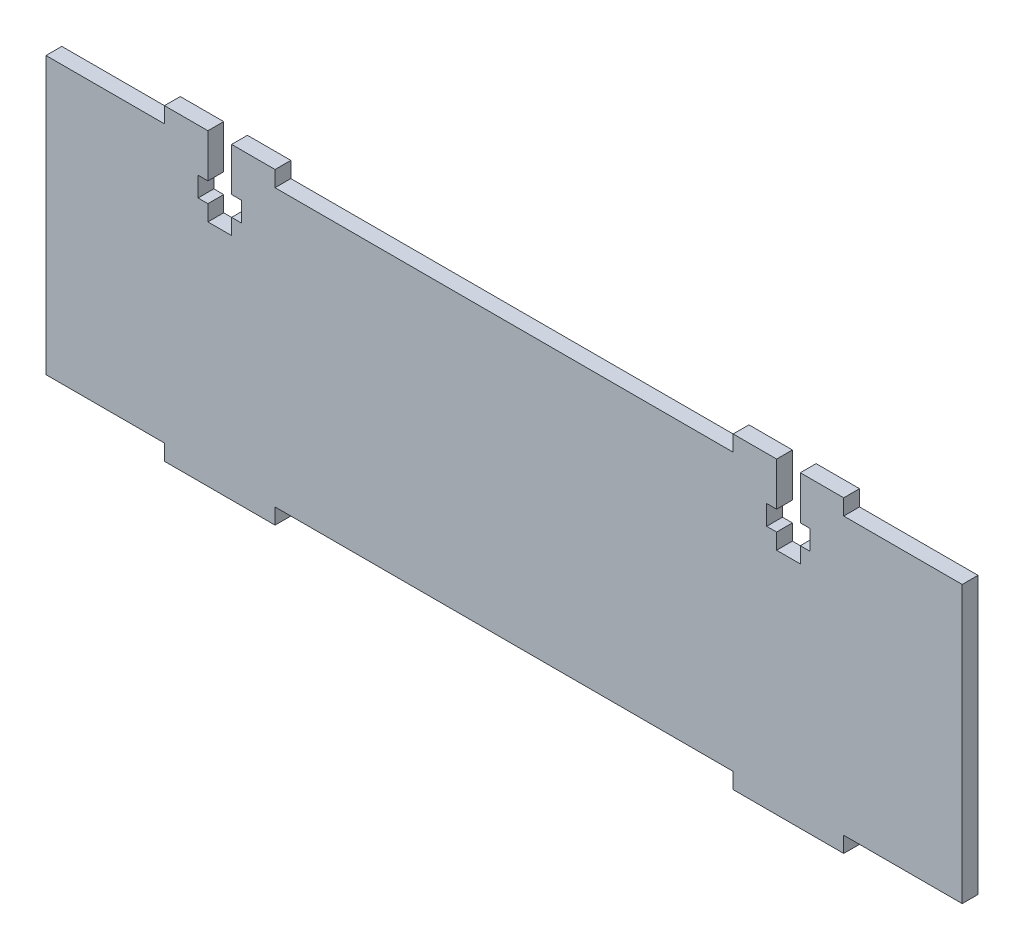
SolidWorks part; units mm, degrees
material "Acrylic (Medium-high impact)"
ref_plane "Front Plane" through (0, 0, 0) normal (0, 0, 1) x (1, 0, 0)
ref_plane "Top Plane" through (0, 0, 0) normal (0, 1, 0) x (1, 0, 0)
ref_plane "Right Plane" through (0, 0, 0) normal (1, 0, 0) x (0, 0, -1)
sketch "Sketch1" plane through (0, 0, 0) normal (0, 0, 1) x (1, 0, 0)
  line L0 (0, 0) -> (15, 0)
  line L1 (116, 0) -> (116, 35)
  line L2 (116, 35) -> (101, 35)
  line L3 (0, 35) -> (0, 0)
  line L4 (15, 35) -> (15, 37)
  line L5 (15, 37) -> (20.5, 37)
  line L6 (15, 0) -> (15, -2)
  line L7 (15, -2) -> (29, -2)
  line L8 (29, 0) -> (29, -2)
  line L9 (29, 0) -> (87, 0)
  line L10 (87, 0) -> (87, -2)
  line L11 (87, 37) -> (92.5, 37)
  line L12 (101, 0) -> (101, -2)
  line L13 (29, 37) -> (23.5, 37)
  line L14 (29, 37) -> (29, 35)
  line L15 (87, 35) -> (87, 37)
  line L16 (92.5, 37) -> (92.5, 31.5)
  line L17 (101, 37) -> (101, 35)
  line L18 (15, 35) -> (0, 35)
  line L19 (87, 35) -> (29, 35)
  line L20 (101, 0) -> (116, 0)
  line L21 (58, 35) -> (58, 0) construction
  line L22 (0, 17.5) -> (116, 17.5) construction
  line L23 (20.5, 37) -> (23.5, 37) construction
  line L24 (22, 37) -> (22, 27) construction
  line L25 (20.5, 37) -> (20.5, 31.5)
  line L26 (20.5, 31.5) -> (19.25, 31.5)
  line L27 (19.25, 31.5) -> (19.25, 29)
  line L28 (19.25, 29) -> (20.5, 29)
  line L29 (20.5, 29) -> (20.5, 27)
  line L30 (20.5, 27) -> (23.5, 27)
  line L31 (23.5, 27) -> (23.5, 29)
  line L32 (23.5, 29) -> (24.75, 29)
  line L33 (24.75, 29) -> (24.75, 31.5)
  line L34 (24.75, 31.5) -> (23.5, 31.5)
  line L35 (23.5, 31.5) -> (23.5, 37)
  line L50 (92.5, 31.5) -> (91.25, 31.5)
  line L51 (91.25, 31.5) -> (91.25, 29)
  line L52 (91.25, 29) -> (92.5, 29)
  line L53 (92.5, 29) -> (92.5, 27)
  line L54 (92.5, 27) -> (95.5, 27)
  line L55 (95.5, 27) -> (95.5, 29)
  line L56 (95.5, 29) -> (96.75, 29)
  line L57 (96.75, 29) -> (96.75, 31.5)
  line L58 (96.75, 31.5) -> (95.5, 31.5)
  line L59 (95.5, 31.5) -> (95.5, 37)
  line L60 (95.5, 37) -> (101, 37)
  line L61 (92.5, 37) -> (95.5, 37) construction
  line L62 (94, 27) -> (94, 37) construction
  line L63 (87, -2) -> (101, -2)
  dimension "D1" = 90
  dimension "D2" = 116
  dimension "D3" = 35
  dimension "D4" = 2
  dimension "D5" = 14
  dimension "D6" = 58
  dimension "D7" = 15
  dimension "D8" = 58
  dimension "D9" = 3
  dimension "D11" = 10
  dimension "D12" = 2.5
  dimension "D13" = 2
  dimension "D15" = 5.5
extrude "Main Slider Side" add sketch "Sketch1" along normal blind 2
